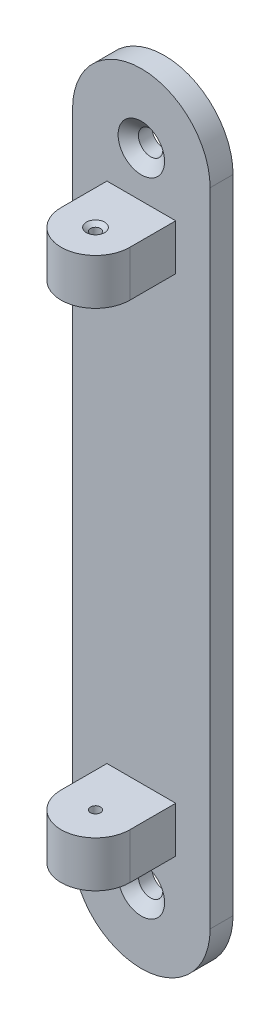
SolidWorks part; units mm, degrees
ref_plane "Front Plane" through (0, 0, 0) normal (0, 0, 1) x (1, 0, 0)
ref_plane "Top Plane" through (0, 0, 0) normal (0, 1, 0) x (1, 0, 0)
ref_plane "Right Plane" through (0, 0, 0) normal (1, 0, 0) x (0, 0, -1)
sketch "Sketch2" plane through (0, 0, 0) normal (0, 0, 1) x (1, 0, 0)
  line L0 (0, 0) -> (0, 88.9)
  line L1 (38.1, 88.9) -> (38.1, 0)
  line L2 (38.1, 0) -> (0, 0)
  arc A0 (0, 88.9) -> (38.1, 88.9) centre (19.05, 88.9) cw
  dimension "D2" = 19.05
  dimension "D1" = 88.9
extrude "Boss-Extrude1" add sketch "Sketch2" along normal blind 6.35
sketch "Sketch4" plane through (0, 0, 6.35) normal (0, 0, 1) x (1, 0, 0)
  point P0 (18.9012, 93.3345)
sketch "Sketch6" plane through (0, 0, 6.35) normal (0, 0, 1) x (1, 0, 0)
  arc A0 (38.1, 88.9) -> (0, 88.9) centre (19.05, 88.9) ccw construction
  point P0 (19.05, 88.9)
hole_wizard "CSK for 1/4 Flat Head Machine Screw (100)2" positions "Sketch6" profile "Sketch7" countersink size "1/4" standard "ANSI Inch" end condition through all
sketch "Sketch7" plane through (19.05, 88.9, 6.35) normal (1, 0, 0) x (0, -1, 0)
  line L0 (0, 0) -> (0, 6.35)
  line L1 (0, 6.35) -> (3.3782, 6.35)
  line L2 (3.3782, 6.35) -> (3.3782, 2.5682)
  line L3 (3.3782, 2.5682) -> (6.4389, 0)
  line L5 (6.4389, 0) -> (0, 0)
  line L6 (-3.3782, 2.5682) -> (-6.4389, 0) construction
  line L11 (0, -6.35) -> (0, 107.95) construction
  dimension "Thru Hole Dia." = 6.7564
  dimension "Thru Hole Depth" = 6.35
  dimension "Near C'Sink Dia." = 12.8778
  dimension "Near C'Sink Angle" = 100
sketch "Sketch8" plane through (0, 0, 6.35) normal (0, 0, 1) x (1, 0, 0)
  line L1 (9.525, 76.2071) -> (28.575, 76.2071)
  line L2 (9.525, 76.2071) -> (9.525, 63.5071)
  line L3 (9.525, 63.5071) -> (28.575, 63.5071)
  line L4 (28.575, 76.2071) -> (28.575, 63.5071)
  line L5 (9.525, 76.2071) -> (28.575, 63.5071) construction
  line L6 (9.525, 63.5071) -> (28.575, 76.2071) construction
  point P5 (0, 0)
  point P6 (0, 0)
  point P12 (0, 0)
extrude "Boss-Extrude2" add sketch "Sketch8" along normal blind 12.7 contours L2 L1 L4 L3
sketch "Sketch10" plane through (0, 76.2071, 0) normal (0, 1, 0) x (1, 0, 0)
  line L0 (9.525, -19.05) -> (28.575, -19.05)
  arc A0 (28.575, -19.05) -> (9.525, -19.05) centre (19.05, -19.05) cw
extrude "Boss-Extrude4" add sketch "Sketch10" against normal blind 12.7 contours A0 L0
sketch "Sketch13" plane through (0, 76.2071, 0) normal (0, 1, 0) x (1, 0, 0)
  arc A0 (9.525, -19.05) -> (28.575, -19.05) centre (19.05, -19.05) ccw construction
  point P0 (19.05, -19.05)
hole_wizard "CSK for #3 Flat Head Machine Screw (100)1" positions "Sketch13" profile "Sketch14" countersink size "#3" standard "ANSI Inch" end condition through all
sketch "Sketch14" plane through (19.05, 76.2071, 19.05) normal (1, 0, 0) x (0, 0, 1)
  line L0 (0, 0) -> (0, 76.2071)
  line L1 (0, 76.2071) -> (1.397, 76.2071)
  line L2 (1.397, 76.2071) -> (1.397, 0.9484)
  line L3 (1.397, 0.9484) -> (2.5273, 0)
  line L5 (2.5273, 0) -> (0, 0)
  line L6 (-1.397, 0.9484) -> (-2.5273, 0) construction
  line L11 (0, -6.35) -> (0, 107.95) construction
  dimension "Thru Hole Dia." = 2.794
  dimension "Thru Hole Depth" = 76.2071
  dimension "Near C'Sink Dia." = 5.0546
  dimension "Near C'Sink Angle" = 100
mirror "Mirror1" about plane through (38.1, 0, 6.35) normal (0, 1, 0) of bodies 108
